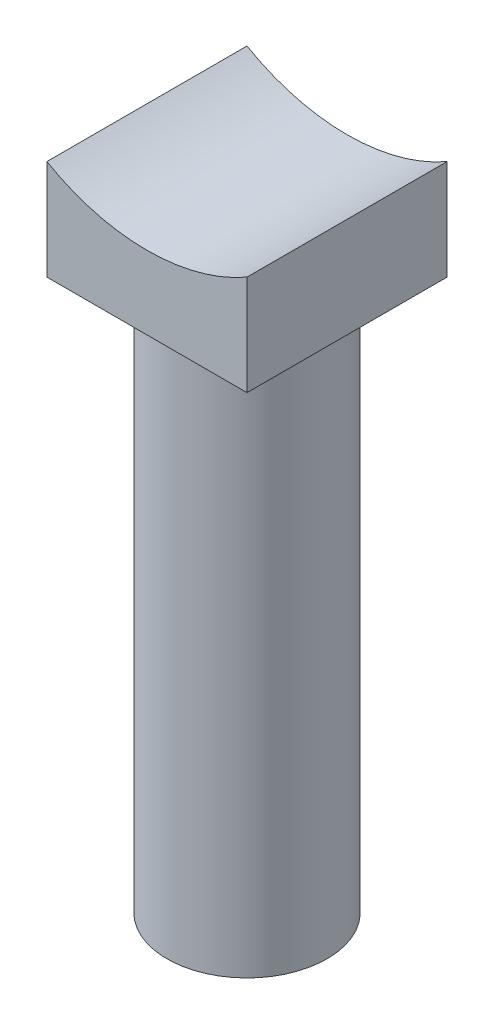
SolidWorks part; units mm, degrees
ref_plane "Front Plane" through (0, 0, 0) normal (0, 0, 1) x (1, 0, 0)
ref_plane "Top Plane" through (0, 0, 0) normal (0, 1, 0) x (1, 0, 0)
ref_plane "Right Plane" through (0, 0, 0) normal (1, 0, 0) x (0, 0, -1)
sketch "Sketch1" plane through (0, 0, 0) normal (0, 0, 1) x (1, 0, 0)
  line L2 (0, 10) -> (0, 0)
  line L3 (0, 0) -> (20, 0)
  line L4 (20, 10) -> (20, 0)
  arc A0 (0, 10) -> (20, 10) centre (10, 27.3205) ccw
  dimension "D3" = 40
  dimension "D1" = 20
  dimension "D2" = 10
extrude "Boss-Extrude1" add sketch "Sketch1" along normal blind 20
sketch "Sketch2" plane through (0, 0, 0) normal (0, -1, 0) x (1, 0, 0)
  line L0 (0, 20) -> (0, 0) construction
  line L2 (0, 20) -> (20, 20) construction
  circle A0 centre (10, 10) radius 8
  point P2 (10, 20)
  point P7 (0, 10)
  dimension "D1" = 16
extrude "Boss-Extrude2" add sketch "Sketch2" along normal blind 55
